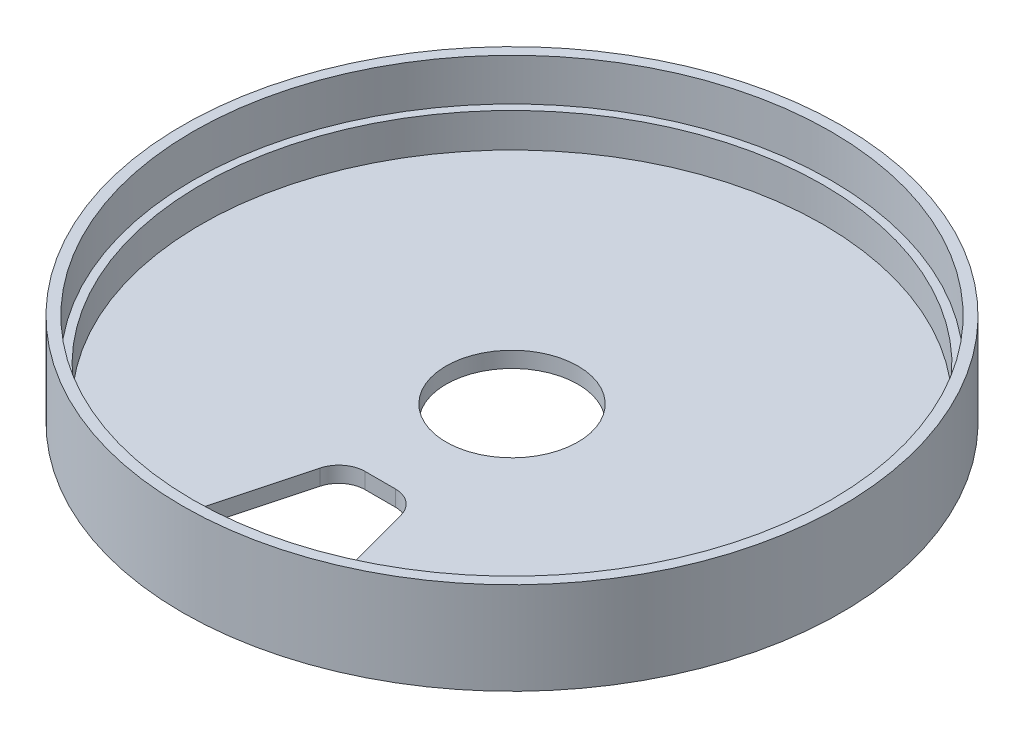
SolidWorks part; units mm, degrees
ref_plane "Front Plane" through (0, 0, 0) normal (0, 0, 1) x (1, 0, 0)
ref_plane "Top Plane" through (0, 0, 0) normal (0, 1, 0) x (1, 0, 0)
ref_plane "Right Plane" through (0, 0, 0) normal (1, 0, 0) x (0, 0, -1)
sketch "Sketch2" plane through (0, 0, 0) normal (0, 0, 1) x (1, 0, 0)
  line L0 (0, 0) -> (0, 207.1312) construction
  line L1 (12.5, 0) -> (62.5, 0)
  line L2 (62.5, 0) -> (62.5, 17.5)
  line L3 (62.5, 17.5) -> (60.5, 17.5)
  line L4 (59, 9.5) -> (59, 3)
  line L5 (59, 3) -> (12.5, 3)
  line L8 (12.5, 3) -> (12.5, 0)
  line L11 (60.5, 17.5) -> (60.5, 9.5)
  line L12 (60.5, 9.5) -> (59, 9.5)
  point P9 (12.5, 1.5)
  dimension "D1" = 12.5
  dimension "D2" = 8
  dimension "D3" = 60.5
  dimension "D5" = 3
  dimension "D6" = 3.5
  dimension "D7" = 17.5
  dimension "D8" = 62.5
revolve "Revolve1" add sketch "Sketch2" angle 360 about L0
sketch "Sketch3" plane through (0, 0, 0) normal (0, -1, 0) x (1, 0, 0)
  line L0 (0, 62.5) -> (0, -62.5) construction
  line L1 (0, 0) -> (-16.1762, 60.3704)
  line L2 (0, 0) -> (16.1762, 60.3704)
  line L3 (-6.6987, 25) -> (6.6987, 25)
  circle A0 centre (0, 0) radius 62.5 construction
  circle A1 centre (0, 0) radius 55
  dimension "D3" = 110
  dimension "D1" = 30
  dimension "D2" = 25
extrude "Cut-Extrude1" cut sketch "Sketch3" against normal through all contours L0 A1 L1 L3 | A1 L0 L3 L2
fillet "Fillet1" radius 5 4 edges at (14.235, 1.5, 53.1259) (-14.235, 1.5, 53.1259) (6.6987, 1.5, 25) (-6.6987, 1.5, 25)
